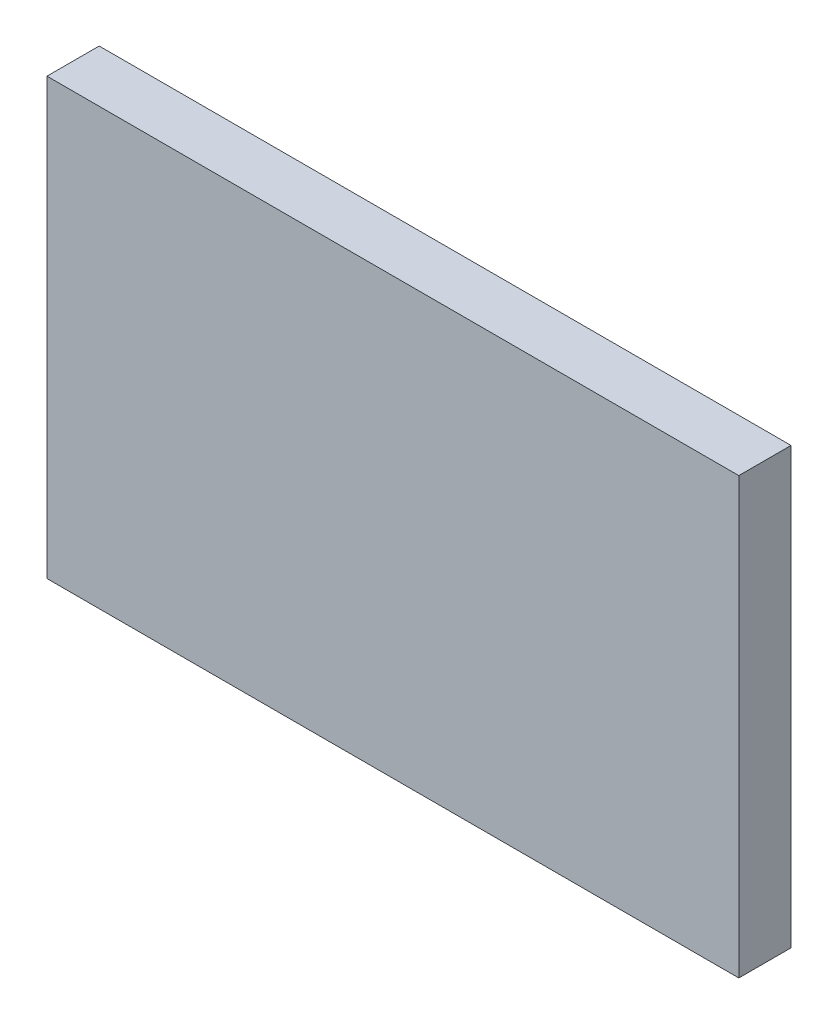
SolidWorks part; units mm, degrees
ref_plane "Alzado" through (0, 0, 0) normal (0, 0, 1) x (1, 0, 0)
ref_plane "Planta" through (0, 0, 0) normal (0, 1, 0) x (1, 0, 0)
ref_plane "Vista lateral" through (0, 0, 0) normal (1, 0, 0) x (0, 0, -1)
sketch "Croquis1" plane through (0, 0, 0) normal (0, 0, 1) x (1, 0, 0)
  line L0 (0, 0) -> (0, 100)
  line L1 (0, 100) -> (159, 100)
  line L2 (159, 100) -> (159, 0)
  line L3 (159, 0) -> (0, 0)
  dimension "D1" = 100
  dimension "D2" = 159
extrude "Saliente-Extruir1" add sketch "Croquis1" along normal blind 12
